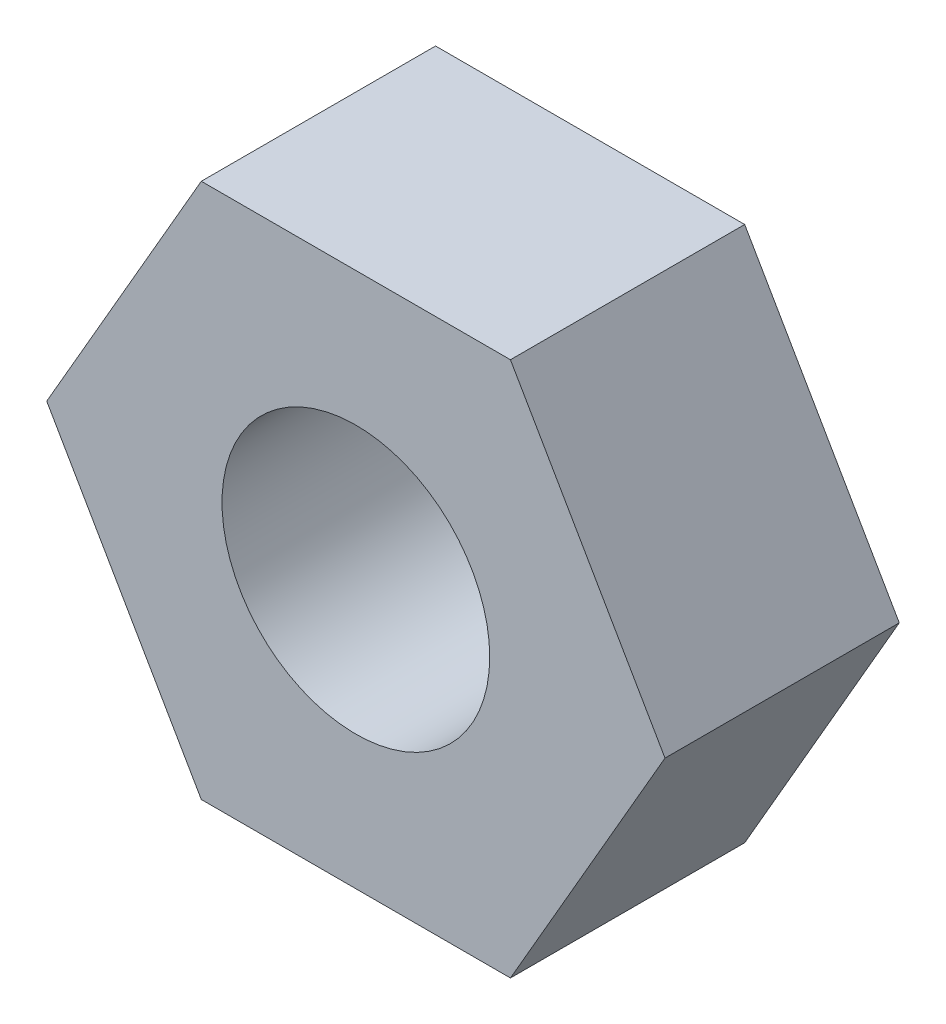
SolidWorks part; units mm, degrees
material "AISI 1035 Steel (SS)"
ref_plane "Front Plane" through (0, 0, 0) normal (0, 0, 1) x (1, 0, 0)
ref_plane "Top Plane" through (0, 0, 0) normal (0, 1, 0) x (1, 0, 0)
ref_plane "Right Plane" through (0, 0, 0) normal (1, 0, 0) x (0, 0, -1)
sketch "Sketch1" plane through (0, 0, 0) normal (0, 0, 1) x (1, 0, 0)
  line L1 (18.4752, 0) -> (9.2376, 16)
  line L2 (9.2376, 16) -> (-9.2376, 16)
  line L3 (-9.2376, 16) -> (-18.4752, 0)
  line L4 (-18.4752, 0) -> (-9.2376, -16)
  line L5 (-9.2376, -16) -> (9.2376, -16)
  line L6 (9.2376, -16) -> (18.4752, 0)
  circle A0 centre (0, 0) radius 16 construction
  circle A1 centre (0, 0) radius 8
  dimension "D1" = 32
  dimension "D2" = 16
extrude "Boss-Extrude1" add sketch "Sketch1" along normal blind 14 contours A1 | L3 L4 L5 L6 L1 L2
